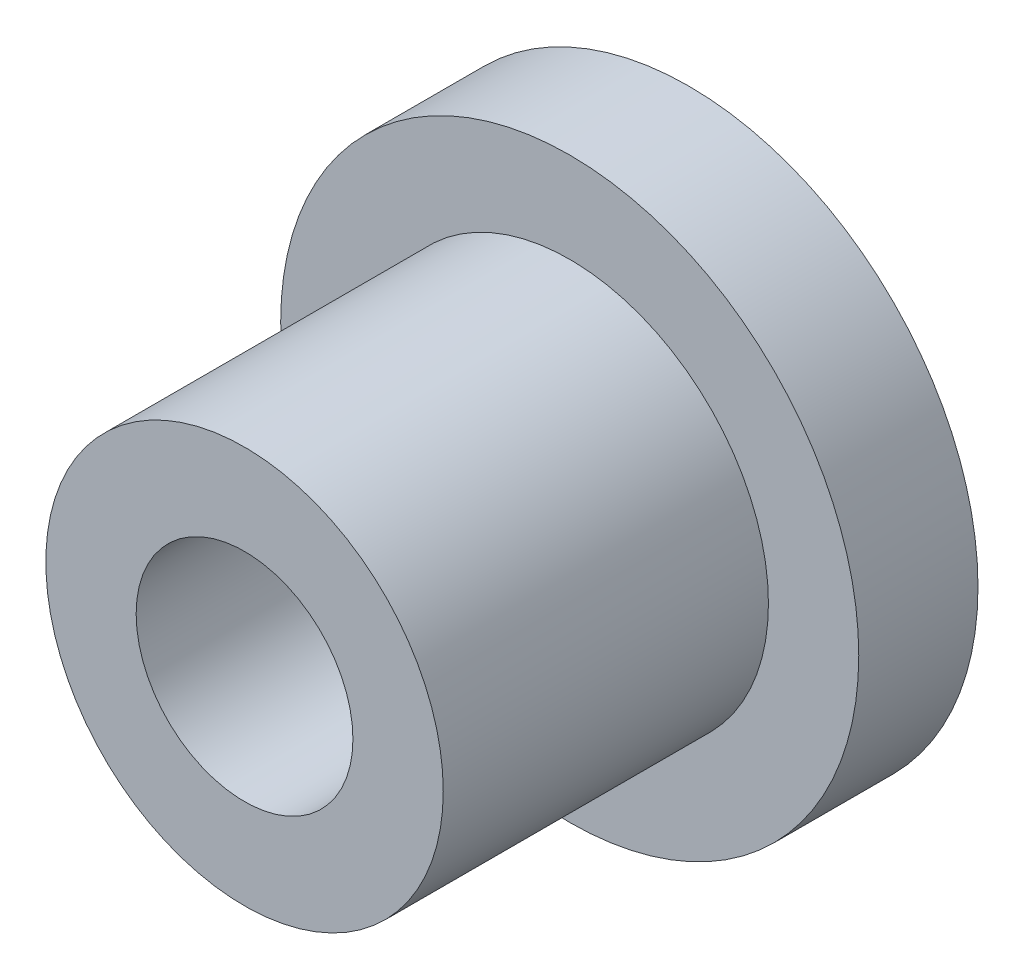
SolidWorks part; units mm, degrees
ref_plane "Front Plane" through (0, 0, 0) normal (0, 0, 1) x (1, 0, 0)
ref_plane "Top Plane" through (0, 0, 0) normal (0, 1, 0) x (1, 0, 0)
ref_plane "Right Plane" through (0, 0, 0) normal (1, 0, 0) x (0, 0, -1)
sketch "Sketch1" plane through (0, 0, 0) normal (0, 0, 1) x (1, 0, 0)
  circle A0 centre (0, 0) radius 8
  dimension "D1" = 16
extrude "Boss-Extrude1" add sketch "Sketch1" along normal blind 3.3
sketch "Sketch2" plane through (0, 0, 3.3) normal (0, 0, 1) x (1, 0, 0)
  circle A0 centre (0, 0) radius 5.5
  dimension "D1" = 11
extrude "Boss-Extrude2" add sketch "Sketch2" along normal blind 9
sketch "Sketch3" plane through (0, 0, 3.3) normal (0, 0, 1) x (1, 0, 0)
  circle A0 centre (0, 0) radius 3
  dimension "D1" = 6
extrude "Cut-Extrude3" cut sketch "Sketch3" against normal through all draft 45 draft outward yes
sketch "Sketch4" plane through (0, 0, 12.3) normal (0, 0, 1) x (1, 0, 0)
  circle A0 centre (0, 0) radius 3
  dimension "D1" = 6
extrude "Cut-Extrude4" cut sketch "Sketch4" against normal through all
